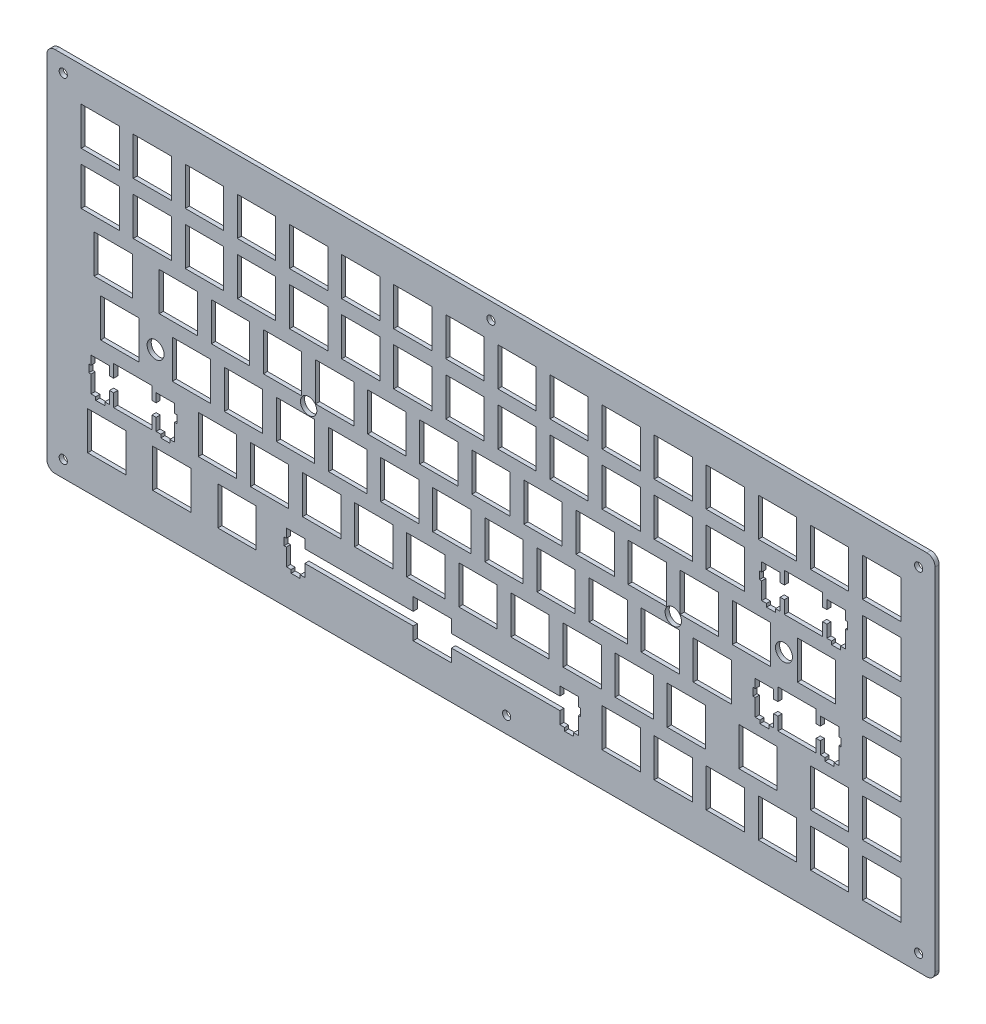
SolidWorks part; units mm, degrees
ref_plane "前视基准面" through (0, 0, 0) normal (0, 0, 1) x (1, 0, 0)
ref_plane "上视基准面" through (0, 0, 0) normal (0, 1, 0) x (1, 0, 0)
ref_plane "右视基准面" through (0, 0, 0) normal (1, 0, 0) x (0, 0, -1)
sketch "草图2" plane through (0, 0, 0) normal (0, 0, 1) x (1, 0, 0)
  line L0 (302.897, 114.558) -> (304.896, 114.558)
  line L1 (304.896, 114.558) -> (304.896, 112.557)
  line L2 (304.896, 2.2572) -> (304.896, 0.2577)
  line L3 (304.896, 0.2577) -> (302.897, 0.2577)
  line L4 (0.0951, 2.2559) -> (0.0951, 0.2577)
  line L5 (0.0951, 0.2577) -> (2.096, 0.2577)
  line L6 (2.096, 114.558) -> (0.0951, 114.558)
  line L7 (0.0951, 114.558) -> (0.0951, 112.557)
  line L20 (304.896, 112.557) -> (304.896, 2.2572)
  line L41 (302.897, 0.2577) -> (2.096, 0.2577)
  line L62 (0.0951, 2.2559) -> (0.0951, 112.557)
  line L83 (2.096, 114.558) -> (302.897, 114.558)
  line L84 (124.062, 16.7831) -> (124.062, 12.0826)
  line L85 (124.062, 12.0826) -> (84.4381, 12.0826)
  line L86 (84.4381, 12.0826) -> (84.4381, 15.3128)
  line L87 (84.4381, 15.3128) -> (77.6884, 15.3128)
  line L88 (77.6884, 15.3128) -> (77.6884, 12.0826)
  line L89 (77.6884, 12.0826) -> (76.8629, 12.0826)
  line L90 (76.8629, 12.0826) -> (76.8629, 9.2838)
  line L91 (76.8629, 9.2838) -> (77.6884, 9.2838)
  line L92 (77.6884, 9.2838) -> (77.6884, 3.0138)
  line L93 (77.6884, 3.0138) -> (79.4135, 3.0138)
  line L94 (79.4135, 3.0138) -> (79.4135, 1.8135)
  line L95 (79.4135, 1.8135) -> (82.714, 1.8135)
  line L96 (82.714, 1.8135) -> (82.714, 3.0138)
  line L97 (82.714, 3.0138) -> (84.4381, 3.0138)
  line L98 (84.4381, 3.0138) -> (84.4381, 7.4827)
  line L99 (84.4381, 7.4827) -> (124.062, 7.4827)
  line L100 (124.062, 7.4827) -> (124.062, 2.7836)
  line L101 (124.062, 2.7836) -> (138.063, 2.7836)
  line L102 (138.063, 2.7836) -> (138.063, 7.4827)
  line L103 (138.063, 7.4827) -> (177.689, 7.4827)
  line L104 (177.689, 7.4827) -> (177.689, 3.0138)
  line L105 (177.689, 3.0138) -> (179.414, 3.0138)
  line L106 (179.414, 3.0138) -> (179.414, 1.8135)
  line L107 (179.414, 1.8135) -> (182.714, 1.8135)
  line L108 (182.714, 1.8135) -> (182.714, 3.0138)
  line L109 (182.714, 3.0138) -> (184.438, 3.0138)
  line L110 (184.438, 3.0138) -> (184.438, 9.2838)
  line L111 (184.438, 9.2838) -> (185.263, 9.2838)
  line L112 (185.263, 9.2838) -> (185.263, 12.0826)
  line L113 (185.263, 12.0826) -> (184.438, 12.0826)
  line L114 (184.438, 12.0826) -> (184.438, 15.3128)
  line L115 (184.438, 15.3128) -> (177.689, 15.3128)
  line L116 (177.689, 15.3128) -> (177.689, 12.0826)
  line L117 (177.689, 12.0826) -> (138.063, 12.0826)
  line L118 (138.063, 12.0826) -> (138.063, 16.7831)
  line L119 (138.063, 16.7831) -> (124.062, 16.7831)
  line L120 (288.371, 16.7831) -> (302.37, 16.7831)
  line L121 (302.37, 16.7831) -> (302.37, 2.7836)
  line L122 (302.37, 2.7836) -> (288.371, 2.7836)
  line L123 (288.371, 2.7836) -> (288.371, 16.7831)
  line L124 (269.321, 16.7831) -> (283.32, 16.7831)
  line L125 (283.32, 16.7831) -> (283.32, 2.7836)
  line L126 (283.32, 2.7836) -> (269.321, 2.7836)
  line L127 (269.321, 2.7836) -> (269.321, 16.7831)
  line L128 (250.271, 16.7831) -> (264.27, 16.7831)
  line L129 (264.27, 16.7831) -> (264.27, 2.7836)
  line L130 (264.27, 2.7836) -> (250.271, 2.7836)
  line L131 (250.271, 2.7836) -> (250.271, 16.7831)
  line L132 (231.221, 16.7831) -> (245.22, 16.7831)
  line L133 (245.22, 16.7831) -> (245.22, 2.7836)
  line L134 (245.22, 2.7836) -> (231.221, 2.7836)
  line L135 (231.221, 2.7836) -> (231.221, 16.7831)
  line L136 (212.171, 16.7831) -> (226.17, 16.7831)
  line L137 (226.17, 16.7831) -> (226.17, 2.7836)
  line L138 (226.17, 2.7836) -> (212.171, 2.7836)
  line L139 (212.171, 2.7836) -> (212.171, 16.7831)
  line L140 (193.121, 16.7831) -> (207.12, 16.7831)
  line L141 (207.12, 16.7831) -> (207.12, 2.7836)
  line L142 (207.12, 2.7836) -> (193.121, 2.7836)
  line L143 (193.121, 2.7836) -> (193.121, 16.7831)
  line L144 (52.626, 16.7831) -> (66.6267, 16.7831)
  line L145 (66.6267, 16.7831) -> (66.6267, 2.7836)
  line L146 (66.6267, 2.7836) -> (52.626, 2.7836)
  line L147 (52.626, 2.7836) -> (52.626, 16.7831)
  line L148 (28.8134, 16.7831) -> (42.8128, 16.7831)
  line L149 (42.8128, 16.7831) -> (42.8128, 2.7836)
  line L150 (42.8128, 2.7836) -> (28.8134, 2.7836)
  line L151 (28.8134, 2.7836) -> (28.8134, 16.7831)
  line L152 (5.0009, 16.7831) -> (19.0018, 16.7831)
  line L153 (19.0018, 16.7831) -> (19.0018, 2.7836)
  line L154 (19.0018, 2.7836) -> (5.0009, 2.7836)
  line L155 (5.0009, 2.7836) -> (5.0009, 16.7831)
  line L156 (14.5259, 35.8316) -> (14.5259, 31.1326)
  line L157 (14.5259, 31.1326) -> (13.0018, 31.1326)
  line L158 (13.0018, 31.1326) -> (13.0018, 34.3628)
  line L159 (13.0018, 34.3628) -> (6.2522, 34.3628)
  line L160 (6.2522, 34.3628) -> (6.2522, 31.1326)
  line L161 (6.2522, 31.1326) -> (5.4267, 31.1326)
  line L162 (5.4267, 31.1326) -> (5.4267, 28.3325)
  line L163 (5.4267, 28.3325) -> (6.2522, 28.3325)
  line L164 (6.2522, 28.3325) -> (6.2522, 22.0638)
  line L165 (6.2522, 22.0638) -> (7.9761, 22.0638)
  line L166 (7.9761, 22.0638) -> (7.9761, 20.8621)
  line L167 (7.9761, 20.8621) -> (11.2765, 20.8621)
  line L168 (11.2765, 20.8621) -> (11.2765, 22.0638)
  line L169 (11.2765, 22.0638) -> (13.0018, 22.0638)
  line L170 (13.0018, 22.0638) -> (13.0018, 26.5327)
  line L171 (13.0018, 26.5327) -> (14.5259, 26.5327)
  line L172 (14.5259, 26.5327) -> (14.5259, 21.8323)
  line L173 (14.5259, 21.8323) -> (28.5268, 21.8323)
  line L174 (28.5268, 21.8323) -> (28.5268, 26.5327)
  line L175 (28.5268, 26.5327) -> (30.0509, 26.5327)
  line L176 (30.0509, 26.5327) -> (30.0509, 22.0638)
  line L177 (30.0509, 22.0638) -> (31.7762, 22.0638)
  line L178 (31.7762, 22.0638) -> (31.7762, 20.8621)
  line L179 (31.7762, 20.8621) -> (35.0766, 20.8621)
  line L180 (35.0766, 20.8621) -> (35.0766, 22.0638)
  line L181 (35.0766, 22.0638) -> (36.8018, 22.0638)
  line L182 (36.8018, 22.0638) -> (36.8018, 28.3325)
  line L183 (36.8018, 28.3325) -> (37.6259, 28.3325)
  line L184 (37.6259, 28.3325) -> (37.6259, 31.1326)
  line L185 (37.6259, 31.1326) -> (36.8018, 31.1326)
  line L186 (36.8018, 31.1326) -> (36.8018, 34.3628)
  line L187 (36.8018, 34.3628) -> (30.0509, 34.3628)
  line L188 (30.0509, 34.3628) -> (30.0509, 31.1326)
  line L189 (30.0509, 31.1326) -> (28.5268, 31.1326)
  line L190 (28.5268, 31.1326) -> (28.5268, 35.8316)
  line L191 (28.5268, 35.8316) -> (14.5259, 35.8316)
  line L192 (288.371, 35.8316) -> (302.37, 35.8316)
  line L193 (302.37, 35.8316) -> (302.37, 21.8323)
  line L194 (302.37, 21.8323) -> (288.371, 21.8323)
  line L195 (288.371, 21.8323) -> (288.371, 35.8316)
  line L196 (269.321, 35.8316) -> (283.32, 35.8316)
  line L197 (283.32, 35.8316) -> (283.32, 21.8323)
  line L198 (283.32, 21.8323) -> (269.321, 21.8323)
  line L199 (269.321, 21.8323) -> (269.321, 35.8316)
  line L200 (243.126, 35.8316) -> (257.127, 35.8316)
  line L201 (257.127, 35.8316) -> (257.127, 21.8323)
  line L202 (257.127, 21.8323) -> (243.126, 21.8323)
  line L203 (243.126, 21.8323) -> (243.126, 35.8316)
  line L204 (216.932, 35.8316) -> (230.933, 35.8316)
  line L205 (230.933, 35.8316) -> (230.933, 21.8323)
  line L206 (230.933, 21.8323) -> (216.932, 21.8323)
  line L207 (216.932, 21.8323) -> (216.932, 35.8316)
  line L208 (197.882, 35.8316) -> (211.883, 35.8316)
  line L209 (211.883, 35.8316) -> (211.883, 21.8323)
  line L210 (211.883, 21.8323) -> (197.882, 21.8323)
  line L211 (197.882, 21.8323) -> (197.882, 35.8316)
  line L212 (178.832, 35.8316) -> (192.833, 35.8316)
  line L213 (192.833, 35.8316) -> (192.833, 21.8323)
  line L214 (192.833, 21.8323) -> (178.832, 21.8323)
  line L215 (178.832, 21.8323) -> (178.832, 35.8316)
  line L216 (159.782, 35.8316) -> (173.783, 35.8316)
  line L217 (173.783, 35.8316) -> (173.783, 21.8323)
  line L218 (173.783, 21.8323) -> (159.782, 21.8323)
  line L219 (159.782, 21.8323) -> (159.782, 35.8316)
  line L220 (140.732, 35.8316) -> (154.733, 35.8316)
  line L221 (154.733, 35.8316) -> (154.733, 21.8323)
  line L222 (154.733, 21.8323) -> (140.732, 21.8323)
  line L223 (140.732, 21.8323) -> (140.732, 35.8316)
  line L224 (121.682, 35.8316) -> (135.683, 35.8316)
  line L225 (135.683, 35.8316) -> (135.683, 21.8323)
  line L226 (135.683, 21.8323) -> (121.682, 21.8323)
  line L227 (121.682, 21.8323) -> (121.682, 35.8316)
  line L228 (102.632, 35.8316) -> (116.633, 35.8316)
  line L229 (116.633, 35.8316) -> (116.633, 21.8323)
  line L230 (116.633, 21.8323) -> (102.632, 21.8323)
  line L231 (102.632, 21.8323) -> (102.632, 35.8316)
  line L232 (83.5822, 35.8316) -> (97.5829, 35.8316)
  line L233 (97.5829, 35.8316) -> (97.5829, 21.8323)
  line L234 (97.5829, 21.8323) -> (83.5822, 21.8323)
  line L235 (83.5822, 21.8323) -> (83.5822, 35.8316)
  line L236 (64.5322, 35.8316) -> (78.5329, 35.8316)
  line L237 (78.5329, 35.8316) -> (78.5329, 21.8323)
  line L238 (78.5329, 21.8323) -> (64.5322, 21.8323)
  line L239 (64.5322, 21.8323) -> (64.5322, 35.8316)
  line L240 (45.4822, 35.8316) -> (59.4829, 35.8316)
  line L241 (59.4829, 35.8316) -> (59.4829, 21.8323)
  line L242 (59.4829, 21.8323) -> (45.4822, 21.8323)
  line L243 (45.4822, 21.8323) -> (45.4822, 35.8316)
  line L244 (257.413, 54.8816) -> (257.413, 50.1826)
  line L245 (257.413, 50.1826) -> (255.888, 50.1826)
  line L246 (255.888, 50.1826) -> (255.888, 53.4127)
  line L247 (255.888, 53.4127) -> (249.138, 53.4127)
  line L248 (249.138, 53.4127) -> (249.138, 50.1826)
  line L249 (249.138, 50.1826) -> (248.313, 50.1826)
  line L250 (248.313, 50.1826) -> (248.313, 47.3826)
  line L251 (248.313, 47.3826) -> (249.138, 47.3826)
  line L252 (249.138, 47.3826) -> (249.138, 41.1124)
  line L253 (249.138, 41.1124) -> (250.863, 41.1124)
  line L254 (250.863, 41.1124) -> (250.863, 39.9122)
  line L255 (250.863, 39.9122) -> (254.163, 39.9122)
  line L256 (254.163, 39.9122) -> (254.163, 41.1124)
  line L257 (254.163, 41.1124) -> (255.888, 41.1124)
  line L258 (255.888, 41.1124) -> (255.888, 45.5828)
  line L259 (255.888, 45.5828) -> (257.413, 45.5828)
  line L260 (257.413, 45.5828) -> (257.413, 40.8824)
  line L261 (257.413, 40.8824) -> (271.413, 40.8824)
  line L262 (271.413, 40.8824) -> (271.413, 45.5828)
  line L263 (271.413, 45.5828) -> (272.939, 45.5828)
  line L264 (272.939, 45.5828) -> (272.939, 41.1124)
  line L265 (272.939, 41.1124) -> (274.664, 41.1124)
  line L266 (274.664, 41.1124) -> (274.664, 39.9122)
  line L267 (274.664, 39.9122) -> (277.964, 39.9122)
  line L268 (277.964, 39.9122) -> (277.964, 41.1124)
  line L269 (277.964, 41.1124) -> (279.688, 41.1124)
  line L270 (279.688, 41.1124) -> (279.688, 47.3826)
  line L271 (279.688, 47.3826) -> (280.513, 47.3826)
  line L272 (280.513, 47.3826) -> (280.513, 50.1826)
  line L273 (280.513, 50.1826) -> (279.688, 50.1826)
  line L274 (279.688, 50.1826) -> (279.688, 53.4127)
  line L275 (279.688, 53.4127) -> (272.939, 53.4127)
  line L276 (272.939, 53.4127) -> (272.939, 50.1826)
  line L277 (272.939, 50.1826) -> (271.413, 50.1826)
  line L278 (271.413, 50.1826) -> (271.413, 54.8816)
  line L279 (271.413, 54.8816) -> (257.413, 54.8816)
  line L280 (288.371, 54.8816) -> (302.37, 54.8816)
  line L281 (302.37, 54.8816) -> (302.37, 40.8824)
  line L282 (302.37, 40.8824) -> (288.371, 40.8824)
  line L283 (288.371, 40.8824) -> (288.371, 54.8816)
  line L284 (226.457, 54.8816) -> (240.458, 54.8816)
  line L285 (240.458, 54.8816) -> (240.458, 40.8824)
  line L286 (240.458, 40.8824) -> (226.457, 40.8824)
  line L287 (226.457, 40.8824) -> (226.457, 54.8816)
  line L288 (207.407, 54.8816) -> (221.408, 54.8816)
  line L289 (221.408, 54.8816) -> (221.408, 40.8824)
  line L290 (221.408, 40.8824) -> (207.407, 40.8824)
  line L291 (207.407, 40.8824) -> (207.407, 54.8816)
  line L292 (188.357, 54.8816) -> (202.358, 54.8816)
  line L293 (202.358, 54.8816) -> (202.358, 40.8824)
  line L294 (202.358, 40.8824) -> (188.357, 40.8824)
  line L295 (188.357, 40.8824) -> (188.357, 54.8816)
  line L296 (169.307, 54.8816) -> (183.308, 54.8816)
  line L297 (183.308, 54.8816) -> (183.308, 40.8824)
  line L298 (183.308, 40.8824) -> (169.307, 40.8824)
  line L299 (169.307, 40.8824) -> (169.307, 54.8816)
  line L300 (150.257, 54.8816) -> (164.258, 54.8816)
  line L301 (164.258, 54.8816) -> (164.258, 40.8824)
  line L302 (164.258, 40.8824) -> (150.257, 40.8824)
  line L303 (150.257, 40.8824) -> (150.257, 54.8816)
  line L304 (131.207, 54.8816) -> (145.208, 54.8816)
  line L305 (145.208, 54.8816) -> (145.208, 40.8824)
  line L306 (145.208, 40.8824) -> (131.207, 40.8824)
  line L307 (131.207, 40.8824) -> (131.207, 54.8816)
  line L308 (112.157, 54.8816) -> (126.158, 54.8816)
  line L309 (126.158, 54.8816) -> (126.158, 40.8824)
  line L310 (126.158, 40.8824) -> (112.157, 40.8824)
  line L311 (112.157, 40.8824) -> (112.157, 54.8816)
  line L312 (93.1072, 54.8816) -> (107.108, 54.8816)
  line L313 (107.108, 54.8816) -> (107.108, 40.8824)
  line L314 (107.108, 40.8824) -> (93.1072, 40.8824)
  line L315 (93.1072, 40.8824) -> (93.1072, 54.8816)
  line L316 (74.0572, 54.8816) -> (88.0579, 54.8816)
  line L317 (88.0579, 54.8816) -> (88.0579, 40.8824)
  line L318 (88.0579, 40.8824) -> (74.0572, 40.8824)
  line L319 (74.0572, 40.8824) -> (74.0572, 54.8816)
  line L320 (55.0072, 54.8816) -> (69.0079, 54.8816)
  line L321 (69.0079, 54.8816) -> (69.0079, 40.8824)
  line L322 (69.0079, 40.8824) -> (55.0072, 40.8824)
  line L323 (55.0072, 40.8824) -> (55.0072, 54.8816)
  line L324 (35.9572, 54.8816) -> (49.9579, 54.8816)
  line L325 (49.9579, 54.8816) -> (49.9579, 40.8824)
  line L326 (49.9579, 40.8824) -> (35.9572, 40.8824)
  line L327 (35.9572, 40.8824) -> (35.9572, 54.8816)
  line L328 (9.7634, 54.8816) -> (23.7629, 54.8816)
  line L329 (23.7629, 54.8816) -> (23.7629, 40.8824)
  line L330 (23.7629, 40.8824) -> (9.7634, 40.8824)
  line L331 (9.7634, 40.8824) -> (9.7634, 54.8816)
  line L332 (288.371, 73.9316) -> (302.37, 73.9316)
  line L333 (302.37, 73.9316) -> (302.37, 59.9324)
  line L334 (302.37, 59.9324) -> (288.371, 59.9324)
  line L335 (288.371, 59.9324) -> (288.371, 73.9316)
  line L336 (264.557, 73.9316) -> (278.558, 73.9316)
  line L337 (278.558, 73.9316) -> (278.558, 59.9324)
  line L338 (278.558, 59.9324) -> (264.557, 59.9324)
  line L339 (264.557, 59.9324) -> (264.557, 73.9316)
  line L340 (240.746, 73.9316) -> (254.744, 73.9316)
  line L341 (254.744, 73.9316) -> (254.744, 59.9324)
  line L342 (254.744, 59.9324) -> (240.746, 59.9324)
  line L343 (240.746, 59.9324) -> (240.746, 73.9316)
  line L344 (221.696, 73.9316) -> (235.695, 73.9316)
  line L345 (235.695, 73.9316) -> (235.695, 59.9324)
  line L346 (235.695, 59.9324) -> (221.696, 59.9324)
  line L347 (221.696, 59.9324) -> (221.696, 73.9316)
  line L348 (202.646, 73.9316) -> (216.645, 73.9316)
  line L349 (216.645, 73.9316) -> (216.645, 59.9324)
  line L350 (216.645, 59.9324) -> (202.646, 59.9324)
  line L351 (202.646, 59.9324) -> (202.646, 73.9316)
  line L352 (183.596, 73.9316) -> (197.595, 73.9316)
  line L353 (197.595, 73.9316) -> (197.595, 59.9324)
  line L354 (197.595, 59.9324) -> (183.596, 59.9324)
  line L355 (183.596, 59.9324) -> (183.596, 73.9316)
  line L356 (164.546, 73.9316) -> (178.545, 73.9316)
  line L357 (178.545, 73.9316) -> (178.545, 59.9324)
  line L358 (178.545, 59.9324) -> (164.546, 59.9324)
  line L359 (164.546, 59.9324) -> (164.546, 73.9316)
  line L360 (145.496, 73.9316) -> (159.495, 73.9316)
  line L361 (159.495, 73.9316) -> (159.495, 59.9324)
  line L362 (159.495, 59.9324) -> (145.496, 59.9324)
  line L363 (145.496, 59.9324) -> (145.496, 73.9316)
  line L364 (126.446, 73.9316) -> (140.445, 73.9316)
  line L365 (140.445, 73.9316) -> (140.445, 59.9324)
  line L366 (140.445, 59.9324) -> (126.446, 59.9324)
  line L367 (126.446, 59.9324) -> (126.446, 73.9316)
  line L368 (107.396, 73.9316) -> (121.395, 73.9316)
  line L369 (121.395, 73.9316) -> (121.395, 59.9324)
  line L370 (121.395, 59.9324) -> (107.396, 59.9324)
  line L371 (107.396, 59.9324) -> (107.396, 73.9316)
  line L372 (88.3461, 73.9316) -> (102.345, 73.9316)
  line L373 (102.345, 73.9316) -> (102.345, 59.9324)
  line L374 (102.345, 59.9324) -> (88.3461, 59.9324)
  line L375 (88.3461, 59.9324) -> (88.3461, 73.9316)
  line L376 (69.2961, 73.9316) -> (83.2954, 73.9316)
  line L377 (83.2954, 73.9316) -> (83.2954, 59.9324)
  line L378 (83.2954, 59.9324) -> (69.2961, 59.9324)
  line L379 (69.2961, 59.9324) -> (69.2961, 73.9316)
  line L380 (50.2461, 73.9316) -> (64.2454, 73.9316)
  line L381 (64.2454, 73.9316) -> (64.2454, 59.9324)
  line L382 (64.2454, 59.9324) -> (50.2461, 59.9324)
  line L383 (50.2461, 59.9324) -> (50.2461, 73.9316)
  line L384 (31.196, 73.9316) -> (45.1954, 73.9316)
  line L385 (45.1954, 73.9316) -> (45.1954, 59.9324)
  line L386 (45.1954, 59.9324) -> (31.196, 59.9324)
  line L387 (31.196, 59.9324) -> (31.196, 73.9316)
  line L388 (7.3822, 73.9316) -> (21.383, 73.9316)
  line L389 (21.383, 73.9316) -> (21.383, 59.9324)
  line L390 (21.383, 59.9324) -> (7.3822, 59.9324)
  line L391 (7.3822, 59.9324) -> (7.3822, 73.9316)
  line L392 (259.796, 92.9816) -> (259.796, 88.2826)
  line L393 (259.796, 88.2826) -> (258.27, 88.2826)
  line L394 (258.27, 88.2826) -> (258.27, 91.5127)
  line L395 (258.27, 91.5127) -> (251.521, 91.5127)
  line L396 (251.521, 91.5127) -> (251.521, 88.2826)
  line L397 (251.521, 88.2826) -> (250.696, 88.2826)
  line L398 (250.696, 88.2826) -> (250.696, 85.4826)
  line L399 (250.696, 85.4826) -> (251.521, 85.4826)
  line L400 (251.521, 85.4826) -> (251.521, 79.2124)
  line L401 (251.521, 79.2124) -> (253.245, 79.2124)
  line L402 (253.245, 79.2124) -> (253.245, 78.0122)
  line L403 (253.245, 78.0122) -> (256.545, 78.0122)
  line L404 (256.545, 78.0122) -> (256.545, 79.2124)
  line L405 (256.545, 79.2124) -> (258.27, 79.2124)
  line L406 (258.27, 79.2124) -> (258.27, 83.6828)
  line L407 (258.27, 83.6828) -> (259.796, 83.6828)
  line L408 (259.796, 83.6828) -> (259.796, 78.9824)
  line L409 (259.796, 78.9824) -> (273.795, 78.9824)
  line L410 (273.795, 78.9824) -> (273.795, 83.6828)
  line L411 (273.795, 83.6828) -> (275.321, 83.6828)
  line L412 (275.321, 83.6828) -> (275.321, 79.2124)
  line L413 (275.321, 79.2124) -> (277.045, 79.2124)
  line L414 (277.045, 79.2124) -> (277.045, 78.0122)
  line L415 (277.045, 78.0122) -> (280.345, 78.0122)
  line L416 (280.345, 78.0122) -> (280.345, 79.2124)
  line L417 (280.345, 79.2124) -> (282.071, 79.2124)
  line L418 (282.071, 79.2124) -> (282.071, 85.4826)
  line L419 (282.071, 85.4826) -> (282.896, 85.4826)
  line L420 (282.896, 85.4826) -> (282.896, 88.2826)
  line L421 (282.896, 88.2826) -> (282.071, 88.2826)
  line L422 (282.071, 88.2826) -> (282.071, 91.5127)
  line L423 (282.071, 91.5127) -> (275.321, 91.5127)
  line L424 (275.321, 91.5127) -> (275.321, 88.2826)
  line L425 (275.321, 88.2826) -> (273.795, 88.2826)
  line L426 (273.795, 88.2826) -> (273.795, 92.9816)
  line L427 (273.795, 92.9816) -> (259.796, 92.9816)
  line L428 (288.371, 92.9816) -> (302.37, 92.9816)
  line L429 (302.37, 92.9816) -> (302.37, 78.9824)
  line L430 (302.37, 78.9824) -> (288.371, 78.9824)
  line L431 (288.371, 78.9824) -> (288.371, 92.9816)
  line L432 (231.221, 92.9816) -> (245.22, 92.9816)
  line L433 (245.22, 92.9816) -> (245.22, 78.9824)
  line L434 (245.22, 78.9824) -> (231.221, 78.9824)
  line L435 (231.221, 78.9824) -> (231.221, 92.9816)
  line L436 (212.171, 92.9816) -> (226.17, 92.9816)
  line L437 (226.17, 92.9816) -> (226.17, 78.9824)
  line L438 (226.17, 78.9824) -> (212.171, 78.9824)
  line L439 (212.171, 78.9824) -> (212.171, 92.9816)
  line L440 (193.121, 92.9816) -> (207.12, 92.9816)
  line L441 (207.12, 92.9816) -> (207.12, 78.9824)
  line L442 (207.12, 78.9824) -> (193.121, 78.9824)
  line L443 (193.121, 78.9824) -> (193.121, 92.9816)
  line L444 (174.071, 92.9816) -> (188.07, 92.9816)
  line L445 (188.07, 92.9816) -> (188.07, 78.9824)
  line L446 (188.07, 78.9824) -> (174.071, 78.9824)
  line L447 (174.071, 78.9824) -> (174.071, 92.9816)
  line L448 (155.021, 92.9816) -> (169.02, 92.9816)
  line L449 (169.02, 92.9816) -> (169.02, 78.9824)
  line L450 (169.02, 78.9824) -> (155.021, 78.9824)
  line L451 (155.021, 78.9824) -> (155.021, 92.9816)
  line L452 (135.971, 92.9816) -> (149.97, 92.9816)
  line L453 (149.97, 92.9816) -> (149.97, 78.9824)
  line L454 (149.97, 78.9824) -> (135.971, 78.9824)
  line L455 (135.971, 78.9824) -> (135.971, 92.9816)
  line L456 (116.92, 92.9816) -> (130.92, 92.9816)
  line L457 (130.92, 92.9816) -> (130.92, 78.9824)
  line L458 (130.92, 78.9824) -> (116.92, 78.9824)
  line L459 (116.92, 78.9824) -> (116.92, 92.9816)
  line L460 (97.8697, 92.9816) -> (111.869, 92.9816)
  line L461 (111.869, 92.9816) -> (111.869, 78.9824)
  line L462 (111.869, 78.9824) -> (97.8697, 78.9824)
  line L463 (97.8697, 78.9824) -> (97.8697, 92.9816)
  line L464 (78.8211, 92.9816) -> (92.8204, 92.9816)
  line L465 (92.8204, 92.9816) -> (92.8204, 78.9824)
  line L466 (92.8204, 78.9824) -> (78.8211, 78.9824)
  line L467 (78.8211, 78.9824) -> (78.8211, 92.9816)
  line L468 (59.7711, 92.9816) -> (73.7704, 92.9816)
  line L469 (73.7704, 92.9816) -> (73.7704, 78.9824)
  line L470 (73.7704, 78.9824) -> (59.7711, 78.9824)
  line L471 (59.7711, 78.9824) -> (59.7711, 92.9816)
  line L472 (40.7211, 92.9816) -> (54.7204, 92.9816)
  line L473 (54.7204, 92.9816) -> (54.7204, 78.9824)
  line L474 (54.7204, 78.9824) -> (40.7211, 78.9824)
  line L475 (40.7211, 78.9824) -> (40.7211, 92.9816)
  line L476 (21.671, 92.9816) -> (35.6704, 92.9816)
  line L477 (35.6704, 92.9816) -> (35.6704, 78.9824)
  line L478 (35.6704, 78.9824) -> (21.671, 78.9824)
  line L479 (21.671, 78.9824) -> (21.671, 92.9816)
  line L480 (2.621, 92.9816) -> (16.6205, 92.9816)
  line L481 (16.6205, 92.9816) -> (16.6205, 78.9824)
  line L482 (16.6205, 78.9824) -> (2.621, 78.9824)
  line L483 (2.621, 78.9824) -> (2.621, 92.9816)
  line L484 (288.371, 112.032) -> (302.37, 112.032)
  line L485 (302.37, 112.032) -> (302.37, 98.0324)
  line L486 (302.37, 98.0324) -> (288.371, 98.0324)
  line L487 (288.371, 98.0324) -> (288.371, 112.032)
  line L488 (269.321, 112.032) -> (283.32, 112.032)
  line L489 (283.32, 112.032) -> (283.32, 98.0324)
  line L490 (283.32, 98.0324) -> (269.321, 98.0324)
  line L491 (269.321, 98.0324) -> (269.321, 112.032)
  line L492 (250.271, 112.032) -> (264.27, 112.032)
  line L493 (264.27, 112.032) -> (264.27, 98.0324)
  line L494 (264.27, 98.0324) -> (250.271, 98.0324)
  line L495 (250.271, 98.0324) -> (250.271, 112.032)
  line L496 (231.221, 112.032) -> (245.22, 112.032)
  line L497 (245.22, 112.032) -> (245.22, 98.0324)
  line L498 (245.22, 98.0324) -> (231.221, 98.0324)
  line L499 (231.221, 98.0324) -> (231.221, 112.032)
  line L500 (212.171, 112.032) -> (226.17, 112.032)
  line L501 (226.17, 112.032) -> (226.17, 98.0324)
  line L502 (226.17, 98.0324) -> (212.171, 98.0324)
  line L503 (212.171, 98.0324) -> (212.171, 112.032)
  line L504 (193.121, 112.032) -> (207.12, 112.032)
  line L505 (207.12, 112.032) -> (207.12, 98.0324)
  line L506 (207.12, 98.0324) -> (193.121, 98.0324)
  line L507 (193.121, 98.0324) -> (193.121, 112.032)
  line L508 (174.071, 112.032) -> (188.07, 112.032)
  line L509 (188.07, 112.032) -> (188.07, 98.0324)
  line L510 (188.07, 98.0324) -> (174.071, 98.0324)
  line L511 (174.071, 98.0324) -> (174.071, 112.032)
  line L512 (155.021, 112.032) -> (169.02, 112.032)
  line L513 (169.02, 112.032) -> (169.02, 98.0324)
  line L514 (169.02, 98.0324) -> (155.021, 98.0324)
  line L515 (155.021, 98.0324) -> (155.021, 112.032)
  line L516 (135.971, 112.032) -> (149.97, 112.032)
  line L517 (149.97, 112.032) -> (149.97, 98.0324)
  line L518 (149.97, 98.0324) -> (135.971, 98.0324)
  line L519 (135.971, 98.0324) -> (135.971, 112.032)
  line L520 (116.92, 112.032) -> (130.92, 112.032)
  line L521 (130.92, 112.032) -> (130.92, 98.0324)
  line L522 (130.92, 98.0324) -> (116.92, 98.0324)
  line L523 (116.92, 98.0324) -> (116.92, 112.032)
  line L524 (97.8697, 112.032) -> (111.869, 112.032)
  line L525 (111.869, 112.032) -> (111.869, 98.0324)
  line L526 (111.869, 98.0324) -> (97.8697, 98.0324)
  line L527 (97.8697, 98.0324) -> (97.8697, 112.032)
  line L528 (78.8211, 112.032) -> (92.8204, 112.032)
  line L529 (92.8204, 112.032) -> (92.8204, 98.0324)
  line L530 (92.8204, 98.0324) -> (78.8211, 98.0324)
  line L531 (78.8211, 98.0324) -> (78.8211, 112.032)
  line L532 (59.7711, 112.032) -> (73.7704, 112.032)
  line L533 (73.7704, 112.032) -> (73.7704, 98.0324)
  line L534 (73.7704, 98.0324) -> (59.7711, 98.0324)
  line L535 (59.7711, 98.0324) -> (59.7711, 112.032)
  line L536 (40.7211, 112.032) -> (54.7204, 112.032)
  line L537 (54.7204, 112.032) -> (54.7204, 98.0324)
  line L538 (54.7204, 98.0324) -> (40.7211, 98.0324)
  line L539 (40.7211, 98.0324) -> (40.7211, 112.032)
  line L540 (21.671, 112.032) -> (35.6704, 112.032)
  line L541 (35.6704, 112.032) -> (35.6704, 98.0324)
  line L542 (35.6704, 98.0324) -> (21.671, 98.0324)
  line L543 (21.671, 98.0324) -> (21.671, 112.032)
  line L544 (2.621, 112.032) -> (16.6205, 112.032)
  line L545 (16.6205, 112.032) -> (16.6205, 98.0324)
  line L546 (16.6205, 98.0324) -> (2.621, 98.0324)
  line L547 (2.621, 98.0324) -> (2.621, 112.032)
  circle A0 centre (259.6505, 66.932) radius 3.1
  circle A1 centre (29.8601, 47.882) radius 3.1
  circle A2 centre (219.1705, 58.0384) radius 3
  circle A3 centre (85.8208, 58.0383) radius 3
extrude "凸台-拉伸1" add sketch "草图2" along normal blind 1.5
sketch "草图3" plane through (0, 0, 1.5) normal (0, 0, 1) x (1, 0, 0)
  line L0 (0.0951, 114.558) -> (0.0951, 0.2577) construction
  line L1 (-9.9049, 124.558) -> (314.896, 124.558)
  line L2 (-9.9049, 124.558) -> (-9.9049, -9.7423)
  line L3 (-9.9049, -9.7423) -> (314.896, -9.7423)
  line L4 (314.896, 124.558) -> (314.896, -9.7423)
  line L5 (0.0951, 0.2577) -> (304.896, 0.2577) construction
  line L6 (304.896, 114.558) -> (0.0951, 114.558) construction
  line L7 (304.896, 0.2577) -> (304.896, 114.558) construction
  line L9 (0.0951, 114.558) -> (304.896, 114.558)
  line L10 (0.0951, 114.558) -> (0.0951, 0.2577)
  line L11 (0.0951, 0.2577) -> (304.896, 0.2577)
  line L12 (304.896, 114.558) -> (304.896, 0.2577)
  dimension "D1" = 10
  dimension "D2" = 10
  dimension "D3" = 10
  dimension "D4" = 10
extrude "凸台-拉伸3" add sketch "草图3" along direction (0, 0, -1) on the side against the normal blind 1.5
sketch "草图4" plane through (0, 0, 1.5) normal (0, 0, 1) x (1, 0, 0)
  line L0 (314.896, 124.558) -> (-9.9049, 124.558) construction
  line L5 (-9.9049, 124.558) -> (-9.9049, -9.7423) construction
  line L7 (314.896, -9.7423) -> (314.896, 124.558) construction
  line L9 (-9.9049, -9.7423) -> (314.896, -9.7423) construction
  circle A0 centre (-3.9049, 118.558) radius 1.5
  circle A1 centre (152.4955, 118.558) radius 1.5
  circle A2 centre (308.896, 118.558) radius 1.5
  circle A5 centre (-3.9049, -3.7423) radius 1.5
  circle A6 centre (158.2364, -3.7423) radius 1.5
  circle A7 centre (308.896, -3.7423) radius 1.5
  point P22 (314.896, 116.2478)
  point P26 (308.3844, -9.7423)
  point P27 (0, 0)
  point P28 (0, 0)
  point P29 (-9.9049, -5.1473)
  point P30 (0, 0)
  dimension "D1" = 6
  dimension "D3" = 6
  dimension "D2" = 6
  dimension "D4" = 6
  dimension "D5" = 6
  dimension "D7" = 6
  dimension "D8" = 6
  dimension "D9" = 6
  dimension "D10" = 6
  dimension "D11" = 6
extrude "切除-拉伸1" cut sketch "草图4" against normal blind 1.5
fillet "圆角1" radius 3 4 edges at (314.896, -9.7423, 0.75) (-9.9049, -9.7423, 0.75) (-9.9049, 124.558, 0.75) (314.896, 124.558, 0.75)
